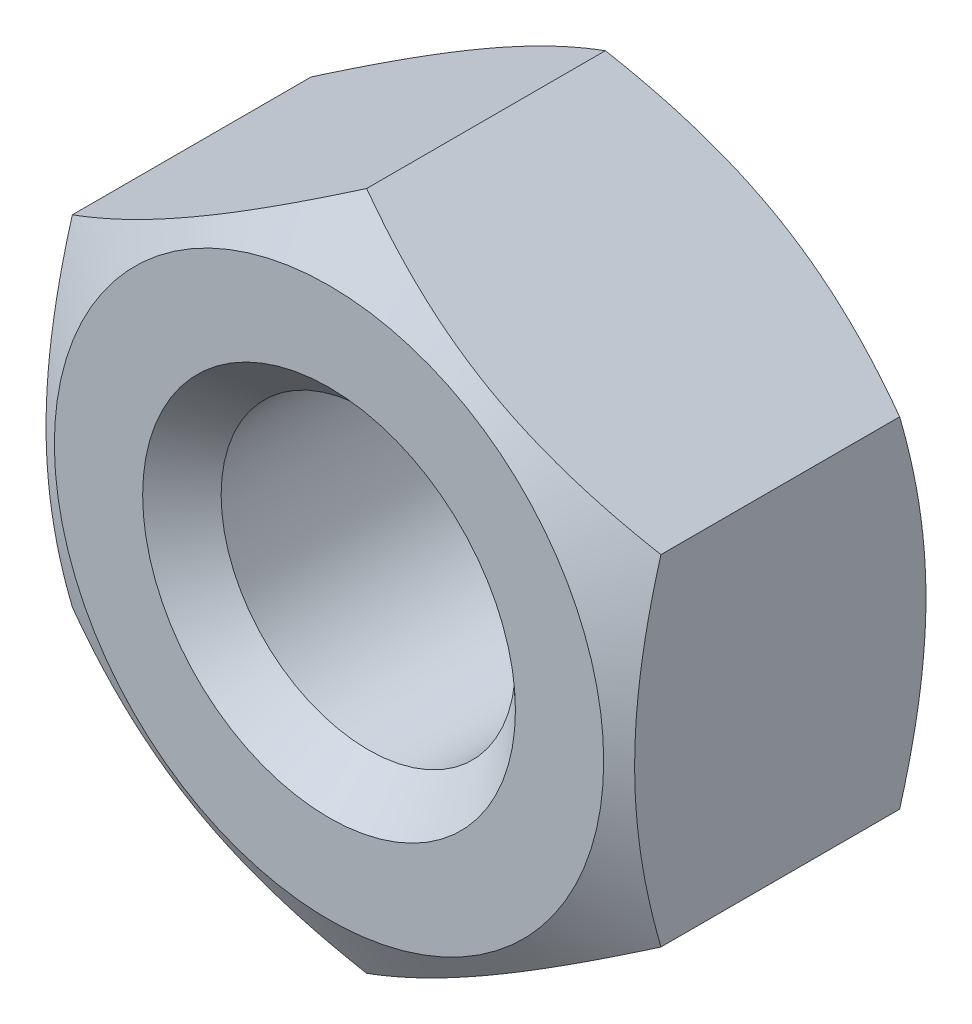
SolidWorks part; units mm, degrees
material "Простая углеродистая сталь"
ref_plane "Спереди" through (0, 0, 0) normal (0, 0, 1) x (1, 0, 0)
ref_plane "Сверху" through (0, 0, 0) normal (0, 1, 0) x (1, 0, 0)
ref_plane "Справа" through (0, 0, 0) normal (1, 0, 0) x (0, 0, -1)
sketch "Эскиз1" plane through (0, 0, 0) normal (0, 1, 0) x (1, 0, 0)
  line L1 (0, 0) -> (-5, 0)
  line L2 (0, 0) -> (0, 3.2)
  line L3 (0, 3.2) -> (-5, 3.2)
  line L4 (-5, 0) -> (-5, 3.2)
  dimension "D1" = 3.2
  dimension "D2" = 5
revolve "Повернуть1" add sketch "Эскиз1" angle 360 about L2
sketch "Эскиз2" plane through (0, 0, 0) normal (0, 0, 1) x (1, 0, 0)
  line L7 (3, -1.7321) -> (3, 1.7321)
  line L8 (3, 1.7321) -> (0, 3.4641)
  line L9 (0, 3.4641) -> (-3, 1.7321)
  line L10 (-3, 1.7321) -> (-3, -1.7321)
  line L11 (-3, -1.7321) -> (0, -3.4641)
  line L12 (0, -3.4641) -> (3, -1.7321)
  circle A0 centre (0, 0) radius 3 construction
  dimension "D1" = 3
extrude "Вырез-Вытянуть1" cut sketch "Эскиз2" against normal up to surface (3.2 mm away) flip side to cut up to face at (5, 0, -3.2)
sketch "Эскиз3" plane through (0, 0, 0) normal (0, 0, 1) x (1, 0, 0)
  circle A0 centre (0, 0) radius 1.5
  dimension "D1" = 3
extrude "Вырез-Вытянуть2" cut sketch "Эскиз3" against normal through all both and the other way through all
sketch "Эскиз4" plane through (0, 0, 0) normal (1, 0, 0) x (0, 0, -1)
  line L0 (0, 2.8) -> (0.3834, 3.4641)
  line L1 (0, 1.7321) -> (0, 3.4641) construction
  line L2 (2.9321, 3.4641) -> (0.2679, 3.4641) construction
  line L3 (0.3834, 3.4641) -> (0, 3.4641)
  line L4 (0, 3.4641) -> (0, 2.8)
  line L5 (1.6, 8.7184) -> (1.6, -2.1993) construction
  line L6 (3.2, 2.8) -> (2.8166, 3.4641)
  line L7 (3.2, 3.4641) -> (3.2, 2.8)
  line L8 (2.8166, 3.4641) -> (3.2, 3.4641)
  line L9 (0, 0) -> (50000, 0) construction
  dimension "D1" = 2.8
  dimension "D2" = 30
  dimension "D3" = 1.6
revolve "Вырез-Повернуть1" cut sketch "Эскиз4" angle 360 about L9
chamfer "Фаска1" distance 0.4 angle 45 2 edges at (-1.5, 0, 0) (1.5, 0, -3.2)
